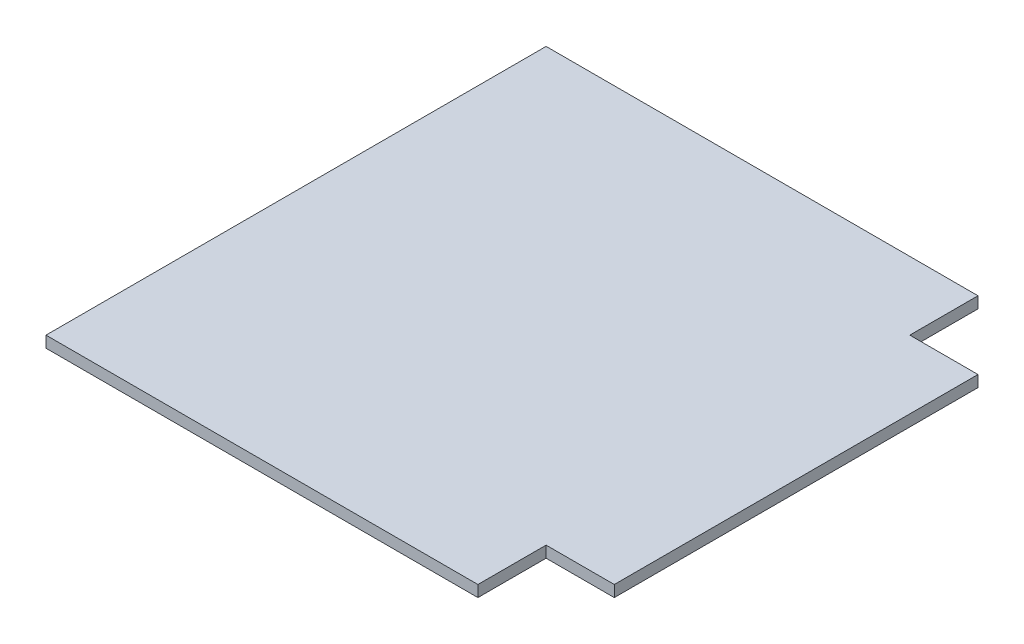
SolidWorks part; units mm, degrees
ref_plane "Alzado" through (0, 0, 0) normal (0, 0, 1) x (1, 0, 0)
ref_plane "Planta" through (0, 0, 0) normal (0, 1, 0) x (1, 0, 0)
ref_plane "Vista lateral" through (0, 0, 0) normal (1, 0, 0) x (0, 0, -1)
sketch "Croquis1" plane through (0, 0, 0) normal (0, 1, 0) x (1, 0, 0)
  line L1 (139.7, -139.7) -> (-139.7, -139.7)
  line L2 (139.7, -139.7) -> (139.7, 139.7)
  line L3 (139.7, 139.7) -> (-139.7, 139.7)
  line L4 (-139.7, -139.7) -> (-139.7, 139.7)
  line L5 (139.7, -139.7) -> (-139.7, 139.7) construction
  line L6 (139.7, 139.7) -> (-139.7, -139.7) construction
  point P0 (0, 0)
  dimension "D1" = 279.4
  dimension "D2" = 279.4
extrude "Saliente-Extruir1" add sketch "Croquis1" along normal blind 6.35
sketch "Croquis3" plane through (0, 6.35, 0) normal (0, 1, 0) x (1, 0, 0)
  line L1 (139.7, -139.7) -> (101.6, -139.7)
  line L2 (139.7, -139.7) -> (139.7, -101.6)
  line L3 (139.7, -101.6) -> (101.6, -101.6)
  line L4 (101.6, -139.7) -> (101.6, -101.6)
  line L5 (139.7, 139.7) -> (101.6, 139.7)
  line L6 (139.7, 139.7) -> (139.7, 101.6)
  line L7 (139.7, 101.6) -> (101.6, 101.6)
  line L8 (101.6, 139.7) -> (101.6, 101.6)
  dimension "D1" = 38.1
  dimension "D2" = 38.1
  dimension "D3" = 38.1
  dimension "D4" = 38.1
extrude "Cortar-Extruir1" cut sketch "Croquis3" against normal through all
